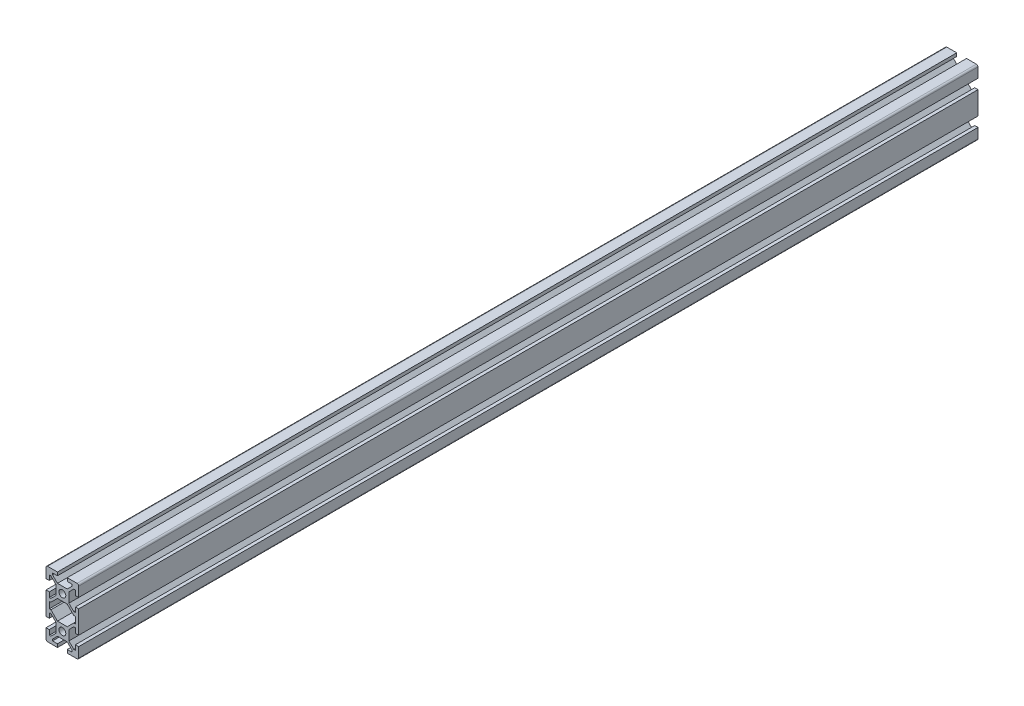
SolidWorks part; units mm, degrees
material "6063-O, Barra estrusa (SS)"
ref_plane "Piano frontale" through (0, 0, 0) normal (0, 0, 1) x (1, 0, 0)
ref_plane "Piano superiore" through (0, 0, 0) normal (0, 1, 0) x (1, 0, 0)
ref_plane "Piano destro" through (0, 0, 0) normal (1, 0, 0) x (0, 0, -1)
other "Lunghezza"
other "Lunghezze"
sketch "Schizzo1" plane through (0, 0, 0) normal (0, 0, 1) x (1, 0, 0)
  line L0 (-6, 18) -> (6, 18) construction
  line L1 (10, 20) -> (-10, 20) construction
  line L2 (10, 20) -> (10, -20) construction
  line L3 (-8, 4) -> (-8, -4) construction
  line L4 (-10, 20) -> (-10, -20) construction
  line L5 (10, 20) -> (-10, 0) construction
  line L6 (10, 0) -> (-10, 20) construction
  line L7 (-3, 14) -> (3, 14) construction
  line L8 (-3, 32.3825) -> (-3, 22.2883) construction
  line L9 (0, 33.8953) -> (0, -6.3729) construction
  line L10 (3, 32.3825) -> (3, 22.2883) construction
  line L11 (-6, 11.8152) -> (-6, 23.4013) construction
  line L12 (6, 10.4596) -> (6, 33.4013) construction
  line L13 (-3, 14) -> (-9, 20) construction
  line L14 (-10, 20) -> (-3, 20)
  line L15 (-3, 20) -> (-3, 18)
  line L16 (-3, 18) -> (-6, 18)
  line L17 (-6, 18) -> (-6, 17)
  line L18 (-6, 17) -> (-3, 14)
  line L19 (-3, 14) -> (3, 14)
  line L20 (3, 14) -> (9, 20) construction
  line L21 (3, 14) -> (6, 17)
  line L22 (6, 17) -> (6, 18)
  line L23 (6, 18) -> (3, 18)
  line L24 (3, 18) -> (3, 20)
  line L25 (3, 20) -> (10, 20)
  line L26 (10, 20) -> (10, 13)
  line L27 (10, 13) -> (8, 13)
  line L28 (8, 13) -> (8, 16)
  line L29 (8, 16) -> (7, 16)
  line L30 (7, 16) -> (4, 13)
  line L31 (4, 13) -> (4, 7)
  line L32 (4, 7) -> (7, 4)
  line L33 (8, 4) -> (8, 7)
  line L34 (7, 4) -> (8, 4)
  line L35 (8, 7) -> (10, 7)
  line L36 (10, 7) -> (10, 0)
  line L37 (8, 4) -> (8, -4) construction
  line L38 (-7, 4) -> (-7, -4) construction
  line L39 (7, 4) -> (7, -4) construction
  line L40 (3, -6) -> (7, -2)
  line L41 (-3, 6) -> (-7, 2)
  line L42 (3, 6) -> (-3, 6)
  line L43 (3, 6) -> (7, 2)
  line L44 (-3, -6) -> (-7, -2)
  line L45 (-7, -2) -> (-8, -2)
  line L46 (-8, -2) -> (-8, 2)
  line L47 (-8, 2) -> (-7, 2)
  line L48 (-10, 0) -> (-10, 7)
  line L49 (-10, 7) -> (-8, 7)
  line L50 (-8, 7) -> (-8, 4)
  line L51 (-8, 4) -> (-7, 4)
  line L52 (-7, 4) -> (-4, 7)
  line L53 (-4, 7) -> (-4, 13)
  line L54 (-4, 13) -> (-7, 16)
  line L55 (-8, 16) -> (-8, 13)
  line L56 (-7, 16) -> (-8, 16)
  line L57 (-8, 13) -> (-10, 13)
  line L58 (-10, 13) -> (-10, 20)
  line L59 (-19.9461, 0) -> (34.5024, 0) construction
  line L60 (3, -14) -> (9, -20) construction
  line L61 (-3, -14) -> (-9, -20) construction
  line L62 (-3, -14) -> (3, -14) construction
  line L63 (10, 0) -> (-10, -20) construction
  line L64 (10, -20) -> (-10, 0) construction
  line L65 (10, -20) -> (-10, -20) construction
  line L66 (-6, -18) -> (6, -18) construction
  line L67 (-10, -13) -> (-10, -20)
  line L68 (-8, -13) -> (-10, -13)
  line L69 (-7, -16) -> (-8, -16)
  line L70 (-8, -16) -> (-8, -13)
  line L71 (-4, -13) -> (-7, -16)
  line L72 (-4, -7) -> (-4, -13)
  line L73 (-7, -4) -> (-4, -7)
  line L74 (-8, -4) -> (-7, -4)
  line L75 (-8, -7) -> (-8, -4)
  line L76 (-10, -7) -> (-8, -7)
  line L77 (-10, 0) -> (-10, -7)
  line L78 (7, -2) -> (8, -2)
  line L79 (8, -2) -> (8, 2)
  line L80 (8, 2) -> (7, 2)
  line L81 (3, -6) -> (-3, -6)
  line L85 (10, -7) -> (10, 0)
  line L86 (8, -7) -> (10, -7)
  line L87 (7, -4) -> (8, -4)
  line L88 (8, -4) -> (8, -7)
  line L89 (4, -7) -> (7, -4)
  line L90 (4, -13) -> (4, -7)
  line L91 (7, -16) -> (4, -13)
  line L92 (8, -16) -> (7, -16)
  line L93 (8, -13) -> (8, -16)
  line L94 (10, -13) -> (8, -13)
  line L95 (10, -20) -> (10, -13)
  line L96 (3, -20) -> (10, -20)
  line L97 (3, -18) -> (3, -20)
  line L98 (6, -18) -> (3, -18)
  line L99 (6, -17) -> (6, -18)
  line L100 (3, -14) -> (6, -17)
  line L101 (-3, -14) -> (3, -14)
  line L102 (-6, -17) -> (-3, -14)
  line L103 (-6, -18) -> (-6, -17)
  line L104 (-3, -18) -> (-6, -18)
  line L105 (-3, -20) -> (-3, -18)
  line L106 (-10, -20) -> (-3, -20)
  line L107 (-3, 0) -> (-10, 0) [skipped]
  line L108 (-3, 0) -> (-3, -2) [skipped]
  line L109 (3, 0) -> (3, 2) [skipped]
  line L110 (10, 0) -> (3, 0) [skipped]
  line L111 (-6, 3) -> (-6, 2) [skipped]
  line L112 (-6, 2) -> (-3, 2) [skipped]
  line L113 (3, 2) -> (6, 2) [skipped]
  line L114 (6, 2) -> (6, 3) [skipped]
  line L115 (-3, 6) -> (-6, 3) [skipped]
  line L116 (6, 3) -> (3, 6) [skipped]
  circle A0 centre (0, 10) radius 2.1
  circle A1 centre (0, -10) radius 2.1
  point P0 (0, 10)
  point P5 (0, 14)
  point P11 (0, 18)
  point P71 (0, 10)
  dimension "D8" = 4.2
  dimension "D2" = 20
  dimension "D3" = 2
  dimension "D4" = 4
  dimension "D5" = 6
  dimension "D6" = 12
  dimension "D7" = 4
  dimension "D9" = 6
  dimension "D10" = 3
  dimension "D11" = 40
extrude "Estrusione-Estrusione1" add sketch "Schizzo1" along normal blind 550 contours L67 L106 L105 L104 L103 L102 L101 L100 L99 L98 L97 L96 L95 L94 L93 L92 L91 L90 L89 L87 L88 L86 L85 L36 L35 L33 L34 L32 L31 L30 L29 L28 L27 L26 L25 L24 L23 L22 L21 L19 L18 L17 L16 L15 L14 L58 L57 L55 L56 L54 L53
fillet "Raccordo1" radius 1 4 edges at (-10, -20, 275) (10, -20, 275) (-10, 20, 275) (10, 20, 275)
